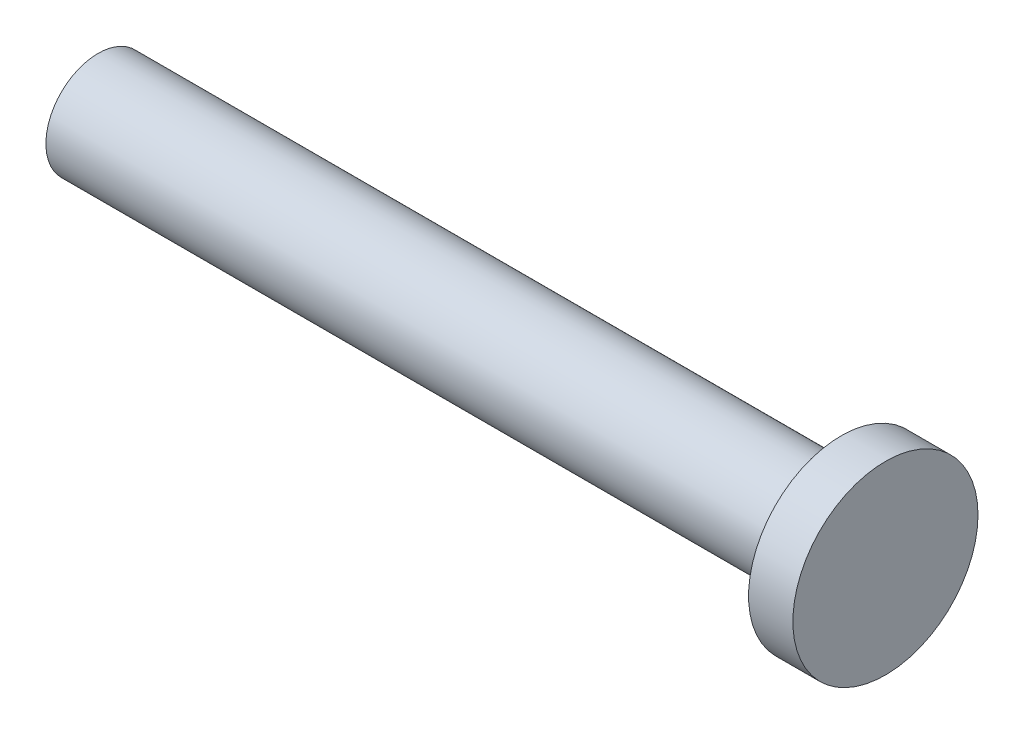
SolidWorks part; units mm, degrees
ref_plane "Front Plane" through (0, 0, 0) normal (0, 0, 1) x (1, 0, 0)
ref_plane "Top Plane" through (0, 0, 0) normal (0, 1, 0) x (1, 0, 0)
ref_plane "Right Plane" through (0, 0, 0) normal (1, 0, 0) x (0, 0, -1)
sketch "Sketch1" plane through (0, 0, 0) normal (1, 0, 0) x (0, 0, -1)
  circle A0 centre (0, 0) radius 10
  dimension "D1" = 20
extrude "Boss-Extrude1" add sketch "Sketch1" along normal blind 142.5
sketch "Sketch2" plane through (142.5, 0, 0) normal (1, 0, 0) x (0, 0, -1)
  circle A0 centre (0, 0) radius 17.75
  dimension "D1" = 35.5
extrude "Boss-Extrude2" add sketch "Sketch2" along normal blind 8.5
